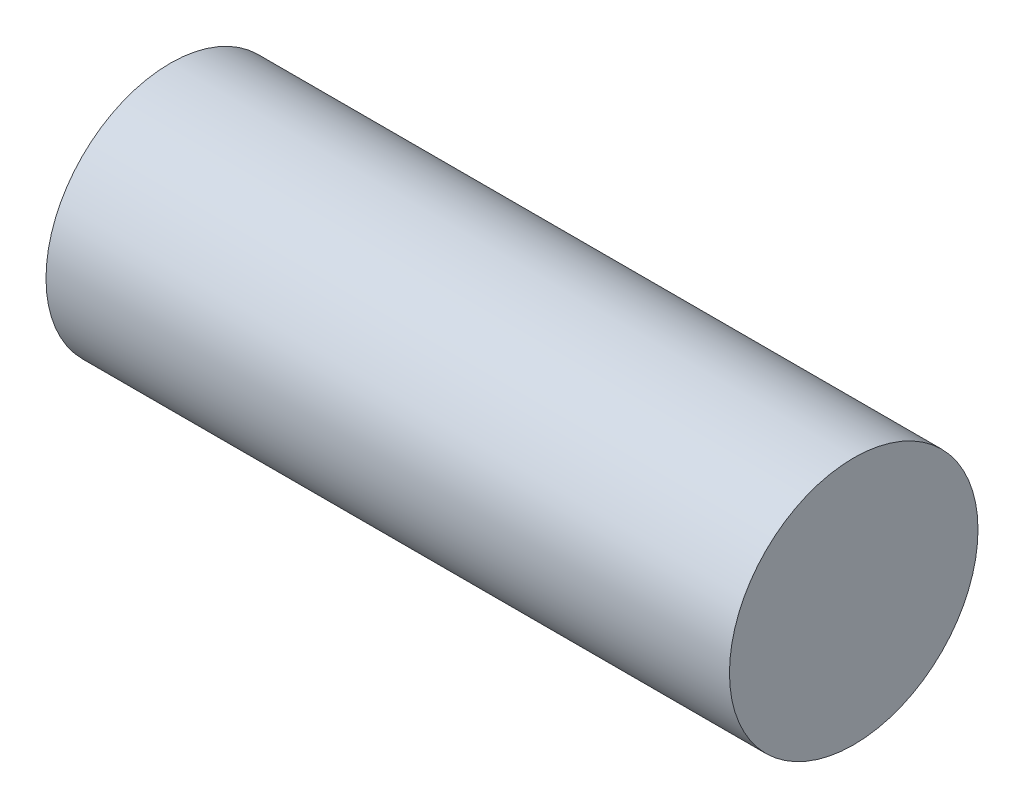
SolidWorks part; units mm, degrees
ref_plane "前视基准面" through (0, 0, 0) normal (0, 0, 1) x (1, 0, 0)
ref_plane "上视基准面" through (0, 0, 0) normal (0, 1, 0) x (1, 0, 0)
ref_plane "右视基准面" through (0, 0, 0) normal (1, 0, 0) x (0, 0, -1)
sketch "草图1" plane through (0, 0, 0) normal (1, 0, 0) x (0, 0, -1)
  circle A0 centre (0, 0) radius 4
  dimension "D1" = 8
extrude "凸台-拉伸1" add sketch "草图1" along normal blind 22
